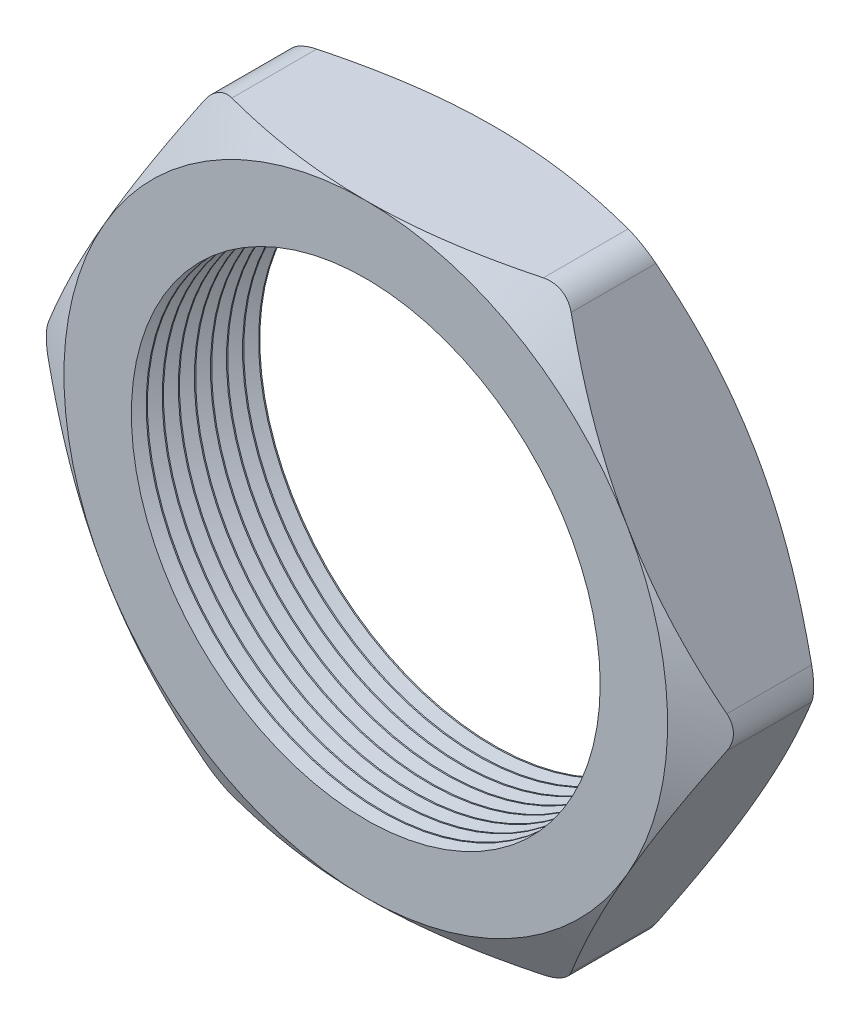
SolidWorks part; units mm, degrees
ref_plane "Front Plane" through (0, 0, 0) normal (0, 0, 1) x (1, 0, 0)
ref_plane "Top Plane" through (0, 0, 0) normal (0, 1, 0) x (1, 0, 0)
ref_plane "Right Plane" through (0, 0, 0) normal (1, 0, 0) x (0, 0, -1)
sketch "Sketch1" plane through (0, 0, 0) normal (0, 0, 1) x (1, 0, 0)
  line L1 (-13.7848, 0) -> (-6.8924, -11.938)
  line L2 (-6.8924, -11.938) -> (6.8924, -11.938)
  line L3 (6.8924, -11.938) -> (13.7848, 0)
  line L4 (13.7848, 0) -> (6.8924, 11.938)
  line L5 (6.8924, 11.938) -> (-6.8924, 11.938)
  line L6 (-6.8924, 11.938) -> (-13.7848, 0)
  circle A0 centre (0, 0) radius 11.938 construction
  circle A1 centre (0, 0) radius 9.271
  dimension "TS" = 18.542
  dimension "H" = 23.876
extrude "Extrude1" add sketch "Sketch1" along normal blind 5.08
sketch "Sketch2" plane through (0, 0, 5.08) normal (0, 0, 1) x (1, 0, 0)
  line L0 (6.8924, 11.938) -> (-6.8924, 11.938) construction
  circle A0 centre (0, 0) radius 11.938
extrude "Cut-Extrude1" cut sketch "Sketch2" against normal through all draft 60 flip side to cut
sketch "Sketch3" plane through (0, 0, 0) normal (0, 0, -1) x (-1, 0, 0)
  line L0 (-6.8924, 11.938) -> (6.8924, 11.938) construction
  circle A0 centre (0, 0) radius 11.938
extrude "Cut-Extrude2" cut sketch "Sketch3" against normal through all draft 60 flip side to cut
fillet "Fillet1" radius 1.27 6 edges at (13.7848, 0, 2.54) (6.8924, -11.938, 2.54) (-6.8924, -11.938, 2.54) (-13.7848, 0, 2.54) (-6.8924, 11.938, 2.54) (6.8924, 11.938, 2.54)
sketch "Sketch4" plane through (0, 0, 0) normal (0, 1, 0) x (1, 0, 0)
  line L0 (-9.271, -5.08) -> (-9.271, -4.4934)
  line L1 (-9.271, 0) -> (-9.271, -5.08) construction
  line L2 (-9.271, -4.4934) -> (-9.779, -4.7867)
  line L3 (-9.779, -4.7867) -> (-9.271, -5.08)
  dimension "D1" = 60
  dimension "D2" = 60
  dimension "D3" = 0.508
revolve "Cut-Revolve1" cut sketch "Sketch4" angle 360 about axis through (0, 0, 0) along (0, 0, 1)
pattern_linear "LPattern1" count 8 spacing 0.635 along (0, 0, -1) of "Cut-Revolve1"
